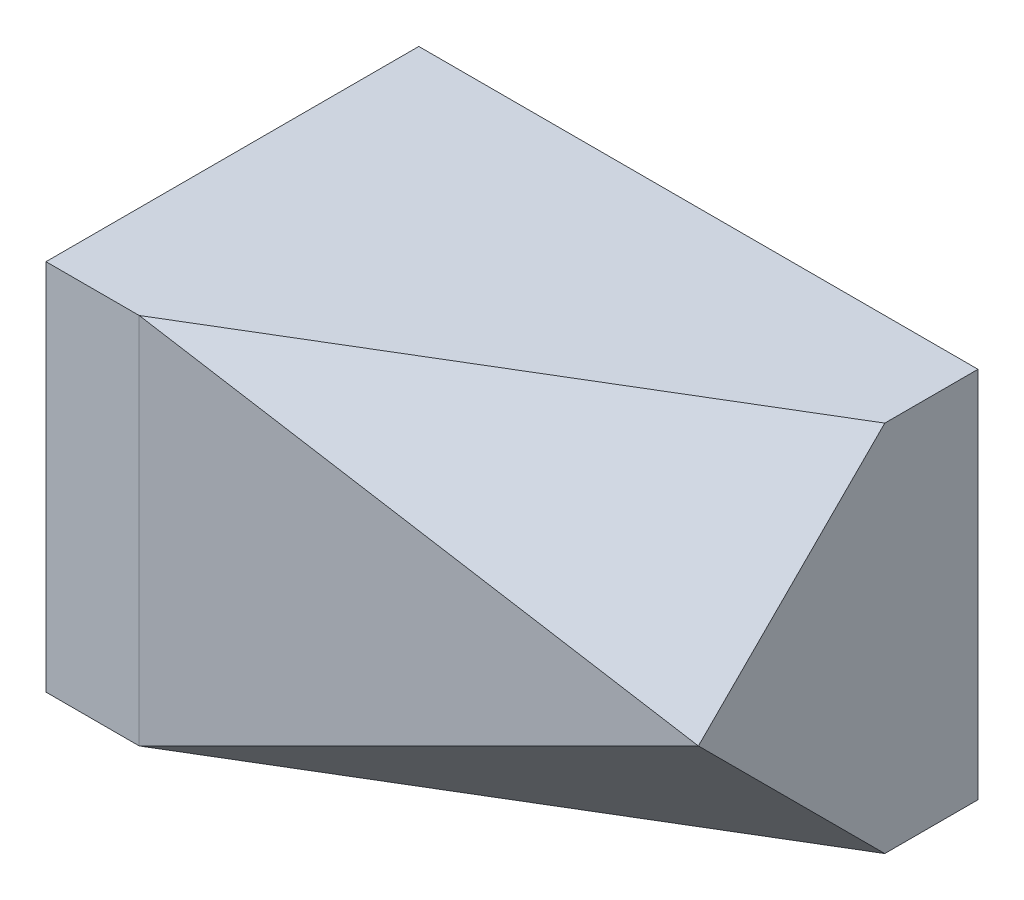
SolidWorks part; units mm, degrees
ref_plane "前基準面" through (0, 0, 0) normal (0, 0, 1) x (1, 0, 0)
ref_plane "上基準面" through (0, 0, 0) normal (0, 1, 0) x (1, 0, 0)
ref_plane "右基準面" through (0, 0, 0) normal (1, 0, 0) x (0, 0, -1)
sketch "草圖1" plane through (0, 0, 0) normal (0, 1, 0) x (1, 0, 0)
  line L0 (15, -5) -> (-10, -10)
  line L1 (15, 10) -> (-15, 10)
  line L2 (15, 10) -> (15, -5)
  line L3 (-10, -10) -> (-15, -10)
  line L4 (-15, 10) -> (-15, -10)
  line L5 (15, 10) -> (-15, -10) construction
  line L6 (9.2308, -6.1538) -> (-15, 10) construction
  point P0 (0, 0)
  dimension "D1" = 20
  dimension "D2" = 30
  dimension "D4" = 5
extrude "填料-伸長1" add sketch "草圖1" along normal blind 20
sketch "草圖2" plane through (0, 20, 0) normal (0, 1, 0) x (1, 0, 0)
  line L0 (-10, -10) -> (15, 5)
  line L1 (15, -5) -> (15, 10) construction
  dimension "D1" = 10
sketch "草圖3" plane through (1.5385, 0, 7.6923) normal (0.1961, 0, 0.9806) x (0.9806, 0, -0.1961)
  line L0 (-11.767, 20) -> (13.7281, 10)
  line L1 (13.7281, 20) -> (13.7281, 0) construction
  dimension "D1" = 10
ref_plane "平面1" through (6.1017, 10.1695, 10.1695) normal (0.3906, 0.6509, 0.6509) x (0.9206, -0.2762, -0.2762)
sketch "草圖4" plane through (6.1017, 10.1695, 10.1695) normal (0.3906, 0.6509, 0.6509) x (0.9206, -0.2762, -0.2762)
  line L1 (-18.2612, 0.9303) -> (21.4199, 0.9303)
  line L2 (-18.2612, 0.9303) -> (-18.2612, 20.5233)
  line L3 (-18.2612, 20.5233) -> (21.4199, 20.5233)
  line L4 (21.4199, 0.9303) -> (21.4199, 20.5233)
extrude "除料-伸長1" cut sketch "草圖4" along normal blind 20
sketch "草圖5" plane through (1.5385, 0, 7.6923) normal (0.1961, 0, 0.9806) x (0.9806, 0, -0.1961)
  line L0 (-11.767, 0) -> (13.7281, 10)
sketch "草圖6" plane through (15, 0, 0) normal (1, 0, 0) x (0, 0, -1)
  line L0 (5, 0) -> (-5, 10)
  line L1 (-5, 0) -> (10, 0) construction
  dimension "D1" = 5
ref_plane "平面2" through (1.0169, -1.6949, 1.6949) normal (-0.3906, 0.6509, -0.6509) x (-0.9206, -0.2762, 0.2762)
sketch "草圖7" plane through (1.0169, -1.6949, 1.6949) normal (-0.3906, 0.6509, -0.6509) x (-0.9206, -0.2762, 0.2762)
  line L1 (-56.3425, -4.1826) -> (75.8506, -4.1826)
  line L2 (-56.3425, -4.1826) -> (-56.3425, 26.0191)
  line L3 (-56.3425, 26.0191) -> (75.8506, 26.0191)
  line L4 (75.8506, -4.1826) -> (75.8506, 26.0191)
extrude "除料-伸長2" cut sketch "草圖7" against normal blind 20
